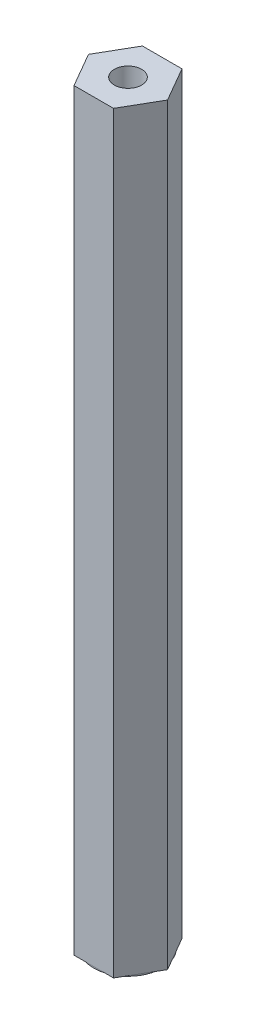
SolidWorks part; units mm, degrees
ref_plane "Front" through (0, 0, 0) normal (0, 0, 1) x (1, 0, 0)
ref_plane "Top" through (0, 0, 0) normal (0, 1, 0) x (1, 0, 0)
ref_plane "Right" through (0, 0, 0) normal (1, 0, 0) x (0, 0, -1)
sketch "Sketch1" plane through (0, 0, 0) normal (0, 1, 0) x (1, 0, 0)
  line L1 (7.3323, 0) -> (3.6662, 6.35)
  line L2 (3.6662, 6.35) -> (-3.6662, 6.35)
  line L3 (-3.6662, 6.35) -> (-7.3323, 0)
  line L4 (-7.3323, 0) -> (-3.6662, -6.35)
  line L5 (-3.6662, -6.35) -> (3.6662, -6.35)
  line L6 (3.6662, -6.35) -> (7.3323, 0)
  circle A0 centre (0, 0) radius 6.35 construction
extrude "Boss-Extrude1" add sketch "Sketch1" along normal blind 139.7
sketch "Sketch2" plane through (0, 139.7, 0) normal (0, 1, 0) x (1, 0, 0)
  circle A0 centre (0, 0) radius 2.54
  dimension "D1" = 5.08
extrude "Cut-Extrude1" cut sketch "Sketch2" against normal blind 25.4
sketch "Sketch3" plane through (0, 0, 0) normal (0, -1, 0) x (1, 0, 0)
  circle A0 centre (0, 0) radius 6.35
extrude "Boss-Extrude2" add sketch "Sketch3" along normal blind 0.254
